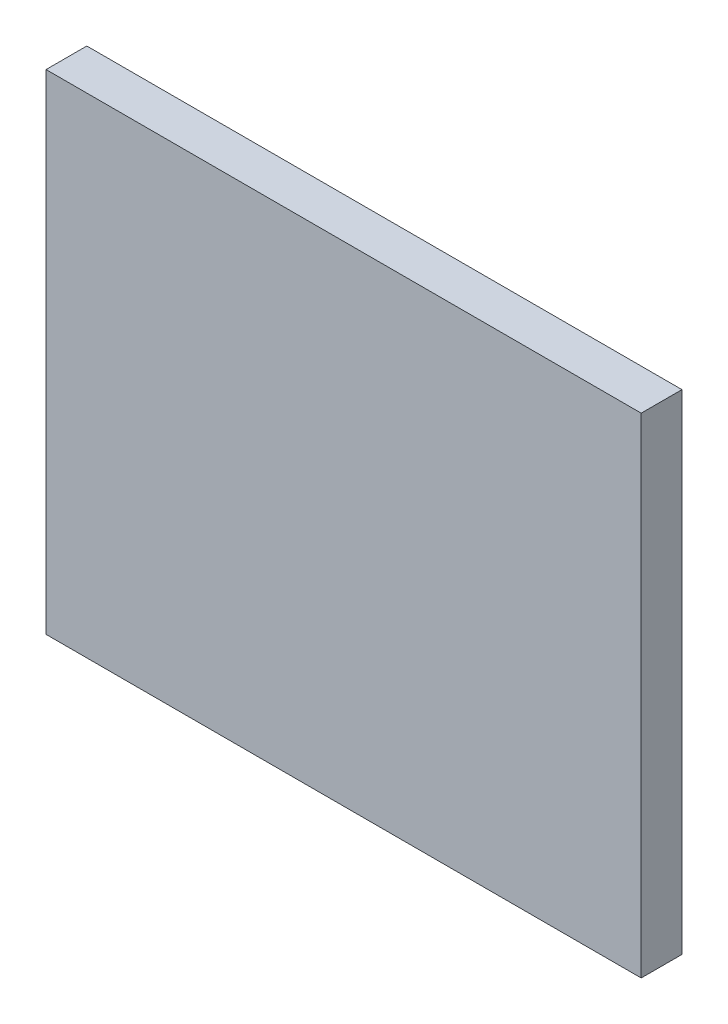
SolidWorks part; units mm, degrees
ref_plane "Plan de face" through (0, 0, 0) normal (0, 0, 1) x (1, 0, 0)
ref_plane "Plan de dessus" through (0, 0, 0) normal (0, 1, 0) x (1, 0, 0)
ref_plane "Plan de droite" through (0, 0, 0) normal (1, 0, 0) x (0, 0, -1)
sketch "Esquisse1" plane through (0, 0, 0) normal (0, 0, 1) x (1, 0, 0)
  line L1 (0, 0) -> (-365, 0)
  line L2 (0, 0) -> (0, 300)
  line L3 (0, 300) -> (-365, 300)
  line L4 (-365, 0) -> (-365, 300)
  dimension "D1" = 365
  dimension "D2" = 300
extrude "Boss.-Extru.1" add sketch "Esquisse1" along normal blind 25
